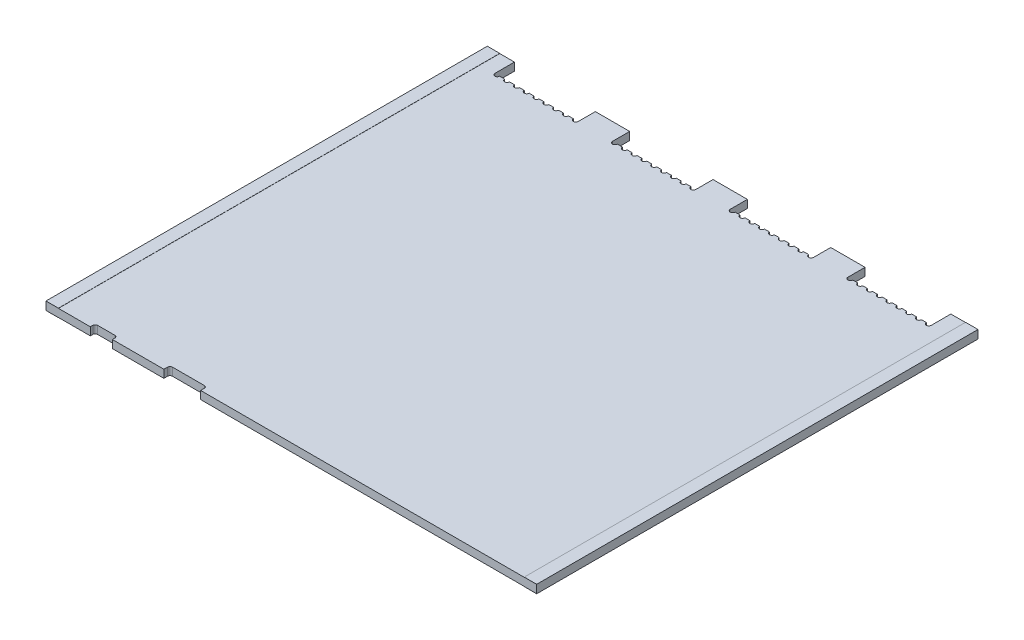
SolidWorks part; units mm, degrees
ref_plane "Front Plane" through (0, 0, 0) normal (0, 0, 1) x (1, 0, 0)
ref_plane "Top Plane" through (0, 0, 0) normal (0, 1, 0) x (1, 0, 0)
ref_plane "Right Plane" through (0, 0, 0) normal (1, 0, 0) x (0, 0, -1)
sketch "Sketch1" plane through (0, 0, 0) normal (0, 1, 0) x (1, 0, 0)
  line B0 (0, 90) -> (5.5, 90)
  line B1 (5.5, 90) -> (5.5, 86)
  line B2 (6.5, 86) -> (7.5, 86)
  line B3 (8.5, 86) -> (9.5, 86)
  line B4 (10.5, 86) -> (11.5, 86)
  line B5 (12.5, 86) -> (13.5, 86)
  line B6 (14.5, 86) -> (15.5, 86)
  line B7 (16.5, 86) -> (17.5, 86)
  line B8 (18.5, 86) -> (19.5, 86)
  line B9 (20.5, 86) -> (21.5, 86)
  line B10 (22.5, 86) -> (22.5, 89.5)
  line B11 (22.5, 89.5) -> (29.5, 89.5)
  line B12 (29.5, 89.5) -> (29.5, 86)
  line B13 (30.5, 86) -> (31.5, 86)
  line B14 (32.5, 86) -> (33.5, 86)
  line B15 (34.5, 86) -> (35.5, 86)
  line B16 (36.5, 86) -> (37.5, 86)
  line B17 (38.5, 86) -> (39.5, 86)
  line B18 (40.5, 86) -> (41.5, 86)
  line B19 (42.5, 86) -> (43.5, 86)
  line B20 (44.5, 86) -> (45.5, 86)
  line B21 (46.5, 86) -> (46.5, 89.5)
  line B22 (46.5, 89.5) -> (53.5, 89.5)
  line B23 (53.5, 89.5) -> (53.5, 86)
  line B24 (54.5, 86) -> (55.5, 86)
  line B25 (56.5, 86) -> (57.5, 86)
  line B26 (58.5, 86) -> (59.5, 86)
  line B27 (60.5, 86) -> (61.5, 86)
  line B28 (62.5, 86) -> (63.5, 86)
  line B29 (64.5, 86) -> (65.5, 86)
  line B30 (66.5, 86) -> (67.5, 86)
  line B31 (68.5, 86) -> (69.5, 86)
  line B32 (70.5, 86) -> (70.5, 89.5)
  line B33 (70.5, 89.5) -> (77.5, 89.5)
  line B34 (77.5, 89.5) -> (77.5, 86)
  line B35 (78.5, 86) -> (79.5, 86)
  line B36 (80.5, 86) -> (81.5, 86)
  line B37 (82.5, 86) -> (83.5, 86)
  line B38 (84.5, 86) -> (85.5, 86)
  line B39 (86.5, 86) -> (87.5, 86)
  line B40 (88.5, 86) -> (89.5, 86)
  line B41 (90.5, 86) -> (91.5, 86)
  line B42 (92.5, 86) -> (93.5, 86)
  line B43 (94.5, 86) -> (94.5, 90)
  line B44 (94.5, 90) -> (100, 90)
  line B45 (100, 90) -> (100, 0)
  line B46 (100, 0) -> (31.5, 0)
  line B47 (31.5, 0) -> (31.5, 0.75)
  line B48 (31, 1.25) -> (24.5, 1.25)
  line B49 (24, 0.75) -> (24, 0)
  line B50 (24, 0) -> (13.5, 0)
  line B51 (13.5, 0) -> (13.5, 0.4375)
  line B52 (13, 1) -> (9.5, 1)
  line B53 (9, 0.5) -> (9, 0)
  line B54 (9, 0) -> (0, 0)
  line B55 (0, 0) -> (0, 90)
  arc B56 (5.5, 86) -> (6.5, 86) centre (6, 86) ccw
  arc B57 (7.5, 86) -> (8.5, 86) centre (8, 86) ccw
  arc B58 (9.5, 86) -> (10.5, 86) centre (10, 86) ccw
  arc B59 (11.5, 86) -> (12.5, 86) centre (12, 86) ccw
  arc B60 (13.5, 86) -> (14.5, 86) centre (14, 86) ccw
  arc B61 (15.5, 86) -> (16.5, 86) centre (16, 86) ccw
  arc B62 (17.5, 86) -> (18.5, 86) centre (18, 86) ccw
  arc B63 (19.5, 86) -> (20.5, 86) centre (20, 86) ccw
  arc B64 (21.5, 86) -> (22.5, 86) centre (22, 86) ccw
  arc B65 (29.5, 86) -> (30.5, 86) centre (30, 86) ccw
  arc B66 (31.5, 86) -> (32.5, 86) centre (32, 86) ccw
  arc B67 (33.5, 86) -> (34.5, 86) centre (34, 86) ccw
  arc B68 (35.5, 86) -> (36.5, 86) centre (36, 86) ccw
  arc B69 (37.5, 86) -> (38.5, 86) centre (38, 86) ccw
  arc B70 (39.5, 86) -> (40.5, 86) centre (40, 86) ccw
  arc B71 (41.5, 86) -> (42.5, 86) centre (42, 86) ccw
  arc B72 (43.5, 86) -> (44.5, 86) centre (44, 86) ccw
  arc B73 (45.5, 86) -> (46.5, 86) centre (46, 86) ccw
  arc B74 (53.5, 86) -> (54.5, 86) centre (54, 86) ccw
  arc B75 (55.5, 86) -> (56.5, 86) centre (56, 86) ccw
  arc B76 (57.5, 86) -> (58.5, 86) centre (58, 86) ccw
  arc B77 (59.5, 86) -> (60.5, 86) centre (60, 86) ccw
  arc B78 (61.5, 86) -> (62.5, 86) centre (62, 86) ccw
  arc B79 (63.5, 86) -> (64.5, 86) centre (64, 86) ccw
  arc B80 (65.5, 86) -> (66.5, 86) centre (66, 86) ccw
  arc B81 (67.5, 86) -> (68.5, 86) centre (68, 86) ccw
  arc B82 (69.5, 86) -> (70.5, 86) centre (70, 86) ccw
  arc B83 (77.5, 86) -> (78.5, 86) centre (78, 86) ccw
  arc B84 (79.5, 86) -> (80.5, 86) centre (80, 86) ccw
  arc B85 (81.5, 86) -> (82.5, 86) centre (82, 86) ccw
  arc B86 (83.5, 86) -> (84.5, 86) centre (84, 86) ccw
  arc B87 (85.5, 86) -> (86.5, 86) centre (86, 86) ccw
  arc B88 (87.5, 86) -> (88.5, 86) centre (88, 86) ccw
  arc B89 (89.5, 86) -> (90.5, 86) centre (90, 86) ccw
  arc B90 (91.5, 86) -> (92.5, 86) centre (92, 86) ccw
  arc B91 (93.5, 86) -> (94.5, 86) centre (94, 86) ccw
  arc B92 (31.5, 0.75) -> (31, 1.25) centre (31, 0.75) ccw
  arc B93 (24.5, 1.25) -> (24, 0.75) centre (24.5, 0.75) ccw
  arc B94 (13.5, 0.4375) -> (13, 1) centre (13.0034, 0.4995) ccw
  arc B95 (9.5, 1) -> (9, 0.5) centre (9.5, 0.5) ccw
sketch_block_instance "BOARD_52-2"
sketch_block "BOARD_52"
extrude "FR4" add sketch "Sketch1" along normal blind 1.6154
sketch "Sketch2" plane through (0, 0, 0) normal (0, 0, 1) x (1, 0, 0)
  line L0 (0, 1.6154) -> (9, 1.6154) construction
  line L1 (2.5, 1.6154) -> (2.5, 1.651)
  line L2 (2.5, 1.651) -> (-0.0356, 1.651)
  line L3 (-0.0356, 1.651) -> (-0.0356, -0.0356)
  line L4 (-0.0356, -0.0356) -> (2.5, -0.0356)
  line L5 (2.5, -0.0356) -> (2.5, 0)
  line L6 (0, 0) -> (9, 0) construction
  line L7 (2.5, 0) -> (0, 0)
  line L8 (0, 0) -> (0, 1.6154)
  line L9 (0, 1.6154) -> (2.5, 1.6154)
  line L10 (-0.0356, 0.9975) -> (0, 0.9975) construction
  line L11 (100, 1.6154) -> (100, 0)
  line L12 (100.0356, -0.0356) -> (100.0356, 1.651)
  line L13 (100.0356, 0.6179) -> (100, 0.6179) construction
  line L14 (97.5, -0.0356) -> (100.0356, -0.0356)
  line L15 (100, 0) -> (97.5, 0)
  line L16 (100.0356, 1.651) -> (97.5, 1.651)
  line L17 (97.5, 1.6154) -> (100, 1.6154)
  line L18 (97.5, 0) -> (97.5, -0.0356)
  line L19 (97.5, 1.651) -> (97.5, 1.6154)
extrude "gold-plating" add sketch "Sketch2" against normal through all separate body
ref_plane "center-of-slot" through (0, 0.8077, 0) normal (0, 1, 0) x (1, 0, 0)
